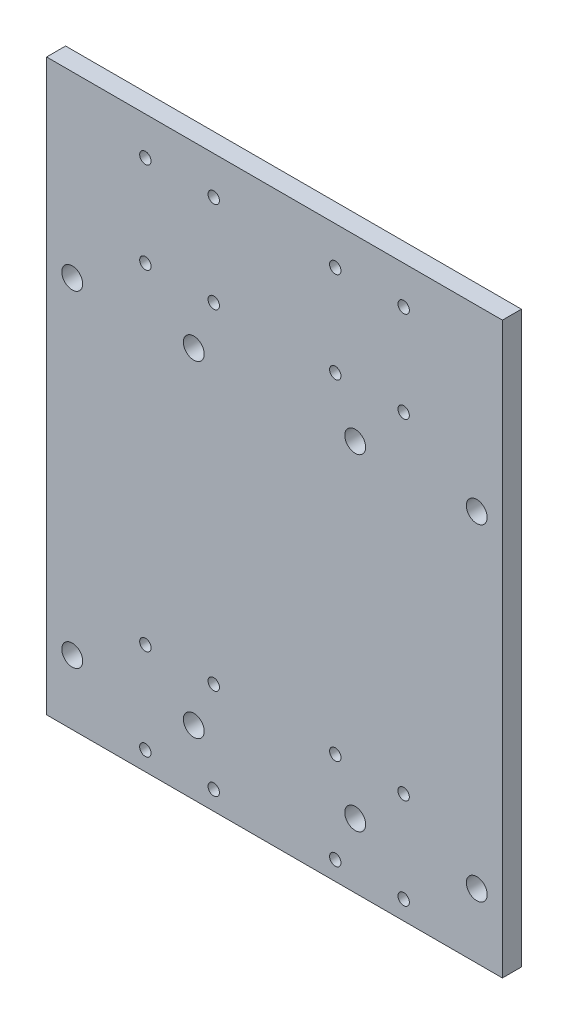
SolidWorks part; units mm, degrees
ref_plane "Front Plane" through (0, 0, 0) normal (0, 0, 1) x (1, 0, 0)
ref_plane "Top Plane" through (0, 0, 0) normal (0, 1, 0) x (1, 0, 0)
ref_plane "Right Plane" through (0, 0, 0) normal (1, 0, 0) x (0, 0, -1)
sketch "Sketch1" plane through (0, 0, 0) normal (0, 0, 1) x (1, 0, 0)
  line L1 (60, -75) -> (-60, -75)
  line L2 (60, -75) -> (60, 75)
  line L3 (60, 75) -> (-60, 75)
  line L4 (-60, -75) -> (-60, 75)
  line L5 (60, -75) -> (-60, 75) construction
  line L6 (60, 75) -> (-60, -75) construction
  point P0 (0, 0)
  dimension "D1" = 120
  dimension "D2" = 150
extrude "Boss-Extrude1" add sketch "Sketch1" along normal blind 5
sketch "Sketch2" plane through (0, 0, 5) normal (0, 0, 1) x (1, 0, 0)
  circle A1 centre (-53.25, 28) radius 2.75
  circle A2 centre (-53.25, 28) radius 2.75
  circle A3 centre (-21.25, 28) radius 2.75
  circle A4 centre (-21.25, 28) radius 2.75
  circle A5 centre (-53.25, -58) radius 2.75
  circle A6 centre (-53.25, -58) radius 2.75
  circle A7 centre (-21.25, -58) radius 2.75
  circle A8 centre (-21.25, -58) radius 2.75
  circle A9 centre (53.25, -58) radius 2.75
  circle A10 centre (53.25, -58) radius 2.75
  circle A11 centre (21.25, -58) radius 2.75
  circle A12 centre (21.25, -58) radius 2.75
  circle A13 centre (53.25, 28) radius 2.75
  circle A14 centre (53.25, 28) radius 2.75
  circle A15 centre (21.25, 28) radius 2.75
  circle A16 centre (21.25, 28) radius 2.75
  dimension "D1" = 0
  dimension "D2" = 0
  dimension "D3" = 0
  dimension "D4" = 0
  dimension "D5" = 0
  dimension "D6" = 0
  dimension "D7" = 0
  dimension "D8" = 0
extrude "rod_holder_mh" cut sketch "Sketch2" against normal through all
sketch "Sketch3" plane through (0, 0, 0) normal (0, 0, -1) x (-1, 0, 0)
  circle A1 centre (34, -70) radius 1.5
  circle A2 centre (34, -70) radius 1.5
  circle A3 centre (34, -46) radius 1.5
  circle A4 centre (34, -46) radius 1.5
  circle A5 centre (16, -70) radius 1.5
  circle A6 centre (16, -70) radius 1.5
  circle A7 centre (16, -46) radius 1.5
  circle A8 centre (16, -46) radius 1.5
  circle A9 centre (-16, -70) radius 1.5
  circle A10 centre (-16, -70) radius 1.5
  circle A11 centre (-16, -46) radius 1.5
  circle A12 centre (-16, -46) radius 1.5
  circle A13 centre (-34, -70) radius 1.5
  circle A14 centre (-34, -70) radius 1.5
  circle A15 centre (-34, -46) radius 1.5
  circle A16 centre (-34, -46) radius 1.5
  circle A17 centre (-16, 41) radius 1.5
  circle A18 centre (-16, 41) radius 1.5
  circle A19 centre (-16, 65) radius 1.5
  circle A20 centre (-16, 65) radius 1.5
  circle A21 centre (-34, 41) radius 1.5
  circle A22 centre (-34, 41) radius 1.5
  circle A23 centre (-34, 65) radius 1.5
  circle A24 centre (-34, 65) radius 1.5
  circle A25 centre (34, 41) radius 1.5
  circle A26 centre (34, 41) radius 1.5
  circle A27 centre (34, 65) radius 1.5
  circle A28 centre (34, 65) radius 1.5
  circle A29 centre (16, 41) radius 1.5
  circle A30 centre (16, 41) radius 1.5
  circle A31 centre (16, 65) radius 1.5
  circle A32 centre (16, 65) radius 1.5
  dimension "D1" = 0
  dimension "D2" = 0
  dimension "D3" = 0
  dimension "D4" = 0
  dimension "D5" = 0
  dimension "D6" = 0
  dimension "D7" = 0
  dimension "D8" = 0
  dimension "D9" = 0
  dimension "D10" = 0
  dimension "D11" = 0
  dimension "D12" = 0
  dimension "D13" = 0
  dimension "D14" = 0
  dimension "D15" = 0
  dimension "D16" = 0
extrude "linear_bearing_mh" cut sketch "Sketch3" against normal through all
